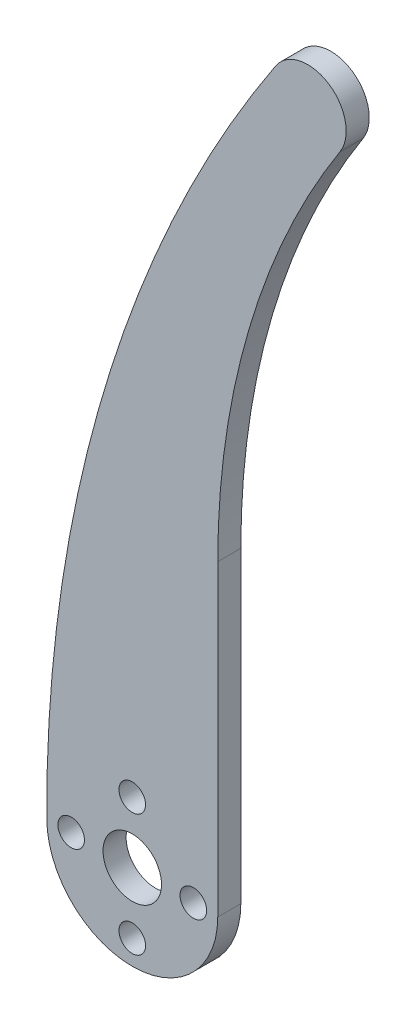
SolidWorks part; units mm, degrees
ref_plane "Plan de face" through (0, 0, 0) normal (0, 0, 1) x (1, 0, 0)
ref_plane "Plan de dessus" through (0, 0, 0) normal (0, 1, 0) x (1, 0, 0)
ref_plane "Plan de droite" through (0, 0, 0) normal (1, 0, 0) x (0, 0, -1)
sketch "Esquisse1" plane through (0, 0, 0) normal (0, 0, 1) x (1, 0, 0)
  line L0 (11.1125, 0) -> (11.1125, 40)
  line L1 (11.1125, 40) -> (111.1125, 40) construction
  line L2 (27.0094, 94.0986) -> (22.8424, 96.8621) construction
  arc A0 (-11.1124, -0.0536) -> (11.1125, 0) centre (0, 0) ccw
  arc A1 (11.1125, 40) -> (27.0094, 94.0986) centre (111.1125, 40) cw
  arc A2 (27.0094, 94.0986) -> (18.6353, 99.5659) centre (22.8038, 96.8038) ccw
  arc A3 (18.6353, 99.5659) -> (-11.1124, -0.0536) centre (167.6764, 0.809) ccw
  point P3 (27.0094, 94.0986)
  dimension "D1" = 40
  dimension "D2" = 100
  dimension "D5" = 5
extrude "Boss.-Extru.3" add sketch "Esquisse1" along normal blind 3
sketch "Esquisse2" plane through (0, 0, 3) normal (0, 0, 1) x (1, 0, 0)
  point P0 (7.9375, 0)
  point P1 (-7.9375, 0)
  point P2 (0, 7.9375)
  point P3 (0, -7.9375)
  dimension "D1" = 15.875
  dimension "D2" = 15.875
  dimension "D3" = 7.9375
  dimension "D4" = 7.9375
hole_wizard "Dégagement #51" positions "Esquisse4" profile "Esquisse3" hole size "#5" standard "Ansi Pouces" end condition through all
sketch "Esquisse4" plane through (0, 0, 3) normal (0, 0, 1) x (1, 0, 0)
  point P1 (-7.9375, 0)
  point P4 (0, 7.9375)
  point P7 (7.9375, 0)
  point P10 (0, -7.9375)
sketch "Esquisse3" plane through (-7.9375, 0, 3) normal (1, 0, 0) x (0, -1, 0)
  line L0 (0, 0) -> (0, 3)
  line L1 (0, 3) -> (1.7272, 3)
  line L2 (1.7272, 3) -> (1.7272, 0)
  line L5 (1.7272, 0) -> (0, 0)
  line L11 (0, -6.35) -> (0, 107.95) construction
  dimension "Diamètre du perçage jusqu'au prochain" = 3.4544
  dimension "Profondeur du perçage jusqu'au prochain" = 3
hole_wizard "Dégagement M71" positions "Esquisse6" profile "Esquisse5" hole size "M7" standard "ISO"
sketch "Esquisse6" plane through (0, 0, 3) normal (0, 0, 1) x (1, 0, 0)
  point P1 (0, 0)
sketch "Esquisse5" plane through (0, 0, 3) normal (1, 0, 0) x (0, -1, 0)
  line L0 (0, 0) -> (0, 9.2933)
  line L1 (0, 9.2933) -> (3.8, 7.01)
  line L2 (3.8, 7.01) -> (3.8, 0)
  line L5 (3.8, 0) -> (0, 0)
  line L10 (0, 9.2933) -> (-3.8, 7.01) construction
  line L11 (0, -6.35) -> (0, 107.95) construction
  dimension "Diamètre du perçage" = 7.6
  dimension "Profondeur du perçage" = 7.01
  dimension "Angle de pointe" = 118
